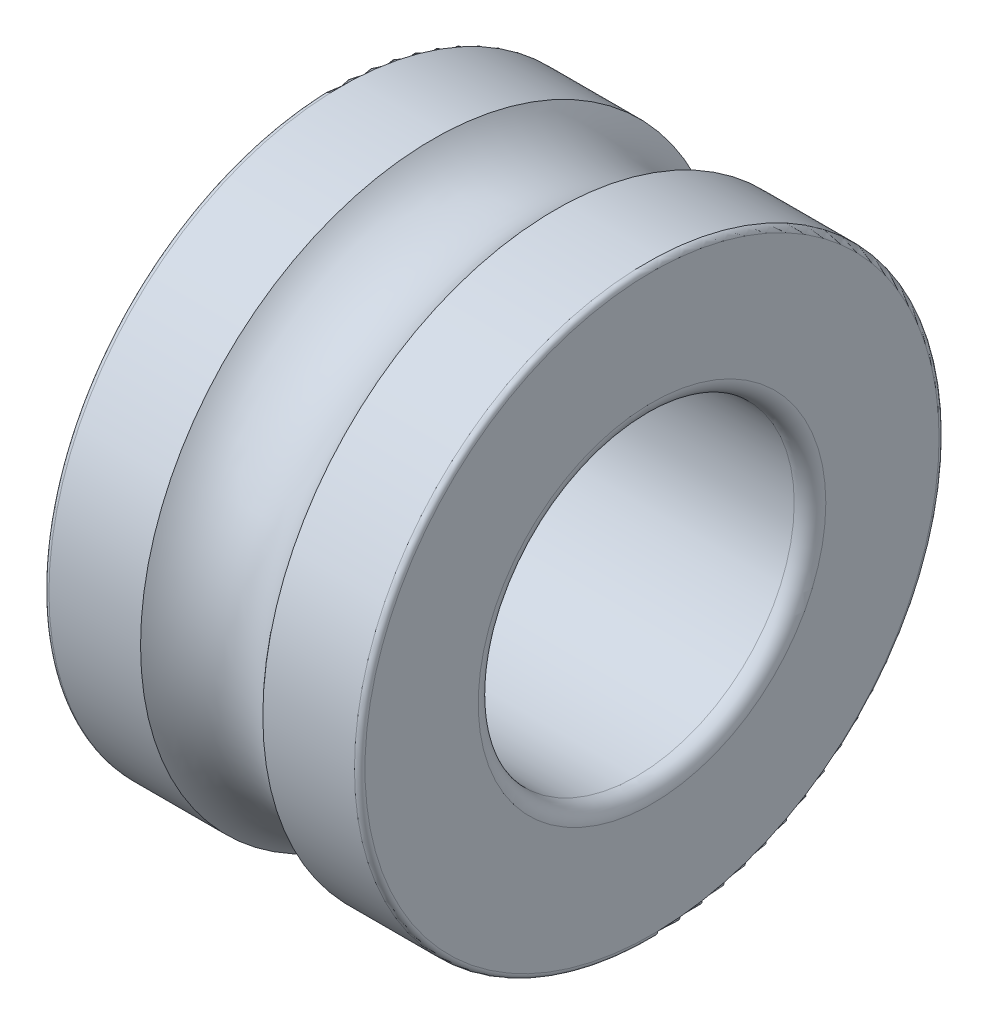
SolidWorks part; units mm, degrees
ref_plane "Front Plane" through (0, 0, 0) normal (0, 0, 1) x (1, 0, 0)
ref_plane "Top Plane" through (0, 0, 0) normal (0, 1, 0) x (1, 0, 0)
ref_plane "Right Plane" through (0, 0, 0) normal (1, 0, 0) x (0, 0, -1)
ref_plane "Plane1" through (0, 0, 0) normal (0, 0, 1) x (1, 0, 0)
sketch "Sketch1" plane through (0, 0, 0) normal (0, 0, 1) x (1, 0, 0)
  line L0 (0.3, 3) -> (5.7, 3)
  line L1 (6, 3.3) -> (6, 5.45)
  line L2 (5.9, 5.55) -> (4.1608, 5.55)
  line L3 (1.8392, 5.55) -> (0.1, 5.55)
  line L4 (0, 5.45) -> (0, 3.3)
  line L5 (5.7, 0) -> (0.3, 0) construction
  arc A0 (0, 3.3) -> (0.3, 3) centre (0.3, 3.3) ccw
  arc A1 (5.7, 3) -> (6, 3.3) centre (5.7, 3.3) ccw
  arc A2 (6, 5.45) -> (5.9, 5.55) centre (5.9, 5.45) ccw
  arc A3 (4.1608, 5.55) -> (1.8392, 5.55) centre (3, 6.5) cw
  arc A4 (0.1, 5.55) -> (0, 5.45) centre (0.1, 5.45) ccw
revolve "Revolve1" add sketch "Sketch1" angle 360 about L5
